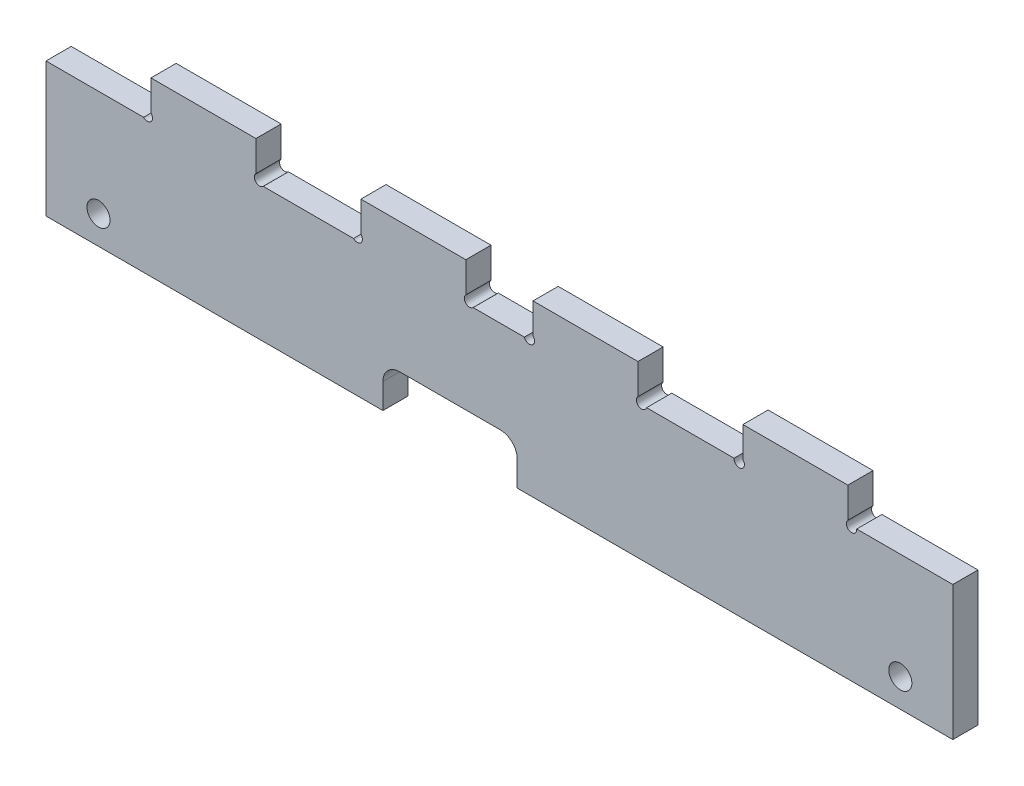
SolidWorks part; units mm, degrees
material "Pino"
ref_plane "Alzado" through (0, 0, 0) normal (0, 0, 1) x (1, 0, 0)
ref_plane "Planta" through (0, 0, 0) normal (0, 1, 0) x (1, 0, 0)
ref_plane "Vista lateral" through (0, 0, 0) normal (1, 0, 0) x (0, 0, -1)
sketch "Croquis1" plane through (0, 0, 0) normal (0, 0, 1) x (1, 0, 0)
  line L1 (-181.0416, 72.6351) -> (-134.5416, 72.6351)
  line L6 (-20.5416, 8.6351) -> (-20.5416, 20.6351)
  line L7 (-12.5416, 28.6351) -> (35.4584, 28.6351)
  line L8 (43.4584, 8.6351) -> (43.4584, 20.6351)
  line L10 (250.9584, 72.6351) -> (250.9584, 8.6351)
  line L13 (-181.0416, 72.6351) -> (-181.0416, 8.6351)
  line L15 (262.9584, 89.6351) -> (200.9584, 89.6351) construction
  line L18 (200.9584, 88.6351) -> (150.9584, 88.6351)
  line L21 (100.9584, 75.1351) -> (100.9584, 89.6351)
  line L22 (100.9584, 89.6351) -> (50.9584, 89.6351)
  line L23 (50.9584, 75.1351) -> (50.9584, 89.6351)
  line L24 (205.1706, 72.6351) -> (250.9584, 72.6351)
  line L25 (105.0669, 72.6351) -> (146.7462, 72.6351)
  line L26 (200.9584, 74.1351) -> (200.9584, 88.6351)
  line L27 (-156.0416, 27.6351) -> (-156.0416, 8.6351) construction
  line L28 (150.9584, 74.1351) -> (150.9584, 88.6351)
  line L29 (250.9584, 8.6351) -> (43.4584, 8.6351)
  line L30 (-181.0416, 8.6351) -> (-20.5416, 8.6351)
  line L31 (18.9584, 76.1351) -> (18.9584, 90.6351)
  line L32 (-131.0416, 76.1351) -> (-131.0416, 90.6351)
  line L33 (-81.0416, 76.1351) -> (-81.0416, 90.6351)
  line L34 (-31.0416, 76.1351) -> (-31.0416, 90.6351)
  line L35 (-131.0416, 90.6351) -> (-81.0416, 90.6351)
  line L36 (-31.0416, 90.6351) -> (18.9584, 90.6351)
  line L37 (22.4584, 72.6351) -> (46.8499, 72.6351)
  line L38 (-77.5416, 72.6351) -> (-34.5416, 72.6351)
  line L39 (-156.0416, 22.1351) -> (-181.0416, 22.1351) construction
  line L40 (-131.0416, 72.6351) -> (-131.0416, 90.6351) construction
  line L41 (-81.0416, 72.6351) -> (-81.0416, 90.6351) construction
  line L42 (-31.0416, 72.6351) -> (-31.0416, 90.6351) construction
  line L43 (18.9584, 72.6351) -> (18.9584, 90.6351) construction
  line L44 (150.9584, 72.6351) -> (150.9584, 88.6351) construction
  line L45 (200.9584, 72.6351) -> (200.9584, 88.6351) construction
  line L46 (225.9584, 8.6351) -> (225.9584, 22.1351) construction
  arc A0 (35.4584, 28.6351) -> (43.4584, 20.6351) centre (35.4584, 20.6351) cw
  arc A1 (-20.5416, 20.6351) -> (-12.5416, 28.6351) centre (-12.5416, 20.6351) cw
  circle A6 centre (-156.0416, 22.1351) radius 5.5
  arc A16 (-134.5416, 72.6351) -> (-131.0416, 76.1351) centre (-132.7916, 74.3851) ccw
  arc A17 (-81.0416, 76.1351) -> (-77.5416, 72.6351) centre (-79.2916, 74.3851) ccw
  arc A18 (-34.5416, 72.6351) -> (-31.0416, 76.1351) centre (-32.7916, 74.3851) ccw
  arc A19 (18.9584, 76.1351) -> (22.4584, 72.6351) centre (20.7084, 74.3851) ccw
  arc A20 (50.9584, 75.1351) -> (46.8499, 72.6351) centre (49.2084, 73.3851) cw
  arc A21 (100.9584, 75.1351) -> (105.0669, 72.6351) centre (102.7084, 73.3851) ccw
  arc A22 (150.9584, 74.1351) -> (146.7462, 72.6351) centre (149.2084, 72.3851) cw
  arc A23 (205.1706, 72.6351) -> (200.9584, 74.1351) centre (202.7084, 72.3851) cw
  circle A25 centre (225.9584, 22.1351) radius 5.5
  point P12 (-20.5416, 28.6351)
  dimension "D6" = 8
  dimension "D7" = 13.5
  dimension "D8" = 25
  dimension "D13" = 19
  dimension "D19" = 25
  dimension "D20" = 11
  dimension "D18" = 2.4749
  dimension "D21" = 50
  dimension "D22" = 32
  dimension "D24" = 432
  dimension "D25" = 160.5
  dimension "D26" = 207.5
  dimension "D11" = 11
  dimension "D3" = 50
  dimension "D4" = 64
  dimension "D5" = 20
  dimension "D9" = 50
  dimension "D10" = 50
  dimension "D15" = 50
  dimension "D16" = 50
  dimension "D17" = 50
  dimension "D23" = 50
  dimension "D29" = 64
  dimension "D30" = 80
  dimension "D31" = 18
extrude "Saliente-Extruir1" add sketch "Croquis1" along normal blind 12
